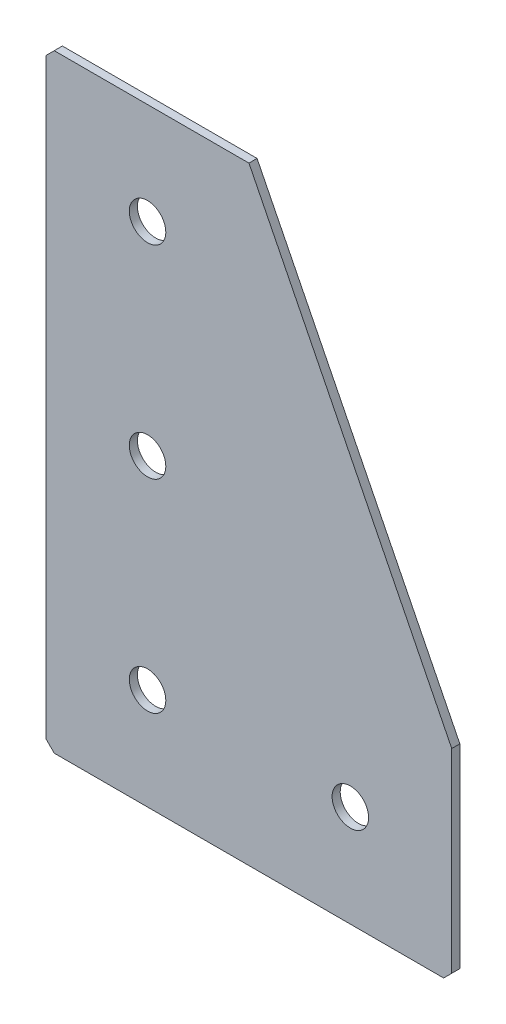
SolidWorks part; units mm, degrees
material "Простая углеродистая сталь"
ref_plane "Спереди(Плоскость XY)" through (0, 0, 0) normal (0, 0, 1) x (1, 0, 0)
ref_plane "Сверху(Плоскость XZ)" through (0, 0, 0) normal (0, 1, 0) x (1, 0, 0)
ref_plane "Справа(Плоскость ZY)" through (0, 0, 0) normal (1, 0, 0) x (0, 0, -1)
sketch "Эскиз1" plane through (0, 0, 0) normal (0, 0, -1) x (1, 0, 0)
  line L0 (0, 0) -> (0, 150)
  line L1 (0, 150) -> (100, 150)
  line L2 (100, 150) -> (100, 100)
  line L3 (100, 100) -> (50, 100) construction
  line L4 (50, 100) -> (50, 0) construction
  line L5 (50, 0) -> (0, 0)
  line L6 (100, 100) -> (50, 0)
  dimension "D1" = 150
  dimension "D2" = 50
  dimension "D3" = 50
  dimension "D4" = 50
extrude "Бобышка-Вытянуть1" add sketch "Эскиз1" along normal blind 2
hole_wizard "Отверстие с зазором M81" positions "Эскиз2" profile "Эскиз3" hole size "M8" standard "DIN" end condition through all
sketch "Эскиз2" plane through (0, 0, -2) normal (0, 0, -1) x (1, 0, 0)
  line L0 (25, 0) -> (25, 150) construction
  line L1 (0, 0) -> (50, 0) construction
  line L2 (100, 150) -> (0, 150) construction
  line L3 (100, 125) -> (0, 125) construction
  line L4 (100, 100) -> (100, 150) construction
  line L5 (0, 150) -> (0, 0) construction
  point P0 (75, 125)
  point P2 (25, 125)
  point P4 (25, 75)
  point P6 (25, 25)
  dimension "D1" = 50
  dimension "D2" = 50
  dimension "D3" = 50
  dimension "D4" = 25
sketch "Эскиз3" plane through (75, -125, -2) normal (1, 0, 0) x (0, 1, 0)
  line L0 (0, 0) -> (0, 2)
  line L1 (0, 2) -> (4.5, 2)
  line L2 (4.5, 2) -> (4.5, 0)
  line L5 (4.5, 0) -> (0, 0)
  line L11 (0, -6.35) -> (0, 107.95) construction
  dimension "Диаметр сквозного отверстия" = 9
  dimension "Глубина сквозного отверстия" = 2
chamfer "Фаска1" distance 2 angle 45 3 edges at (0, 0, -1) (100, -150, -1) (0, -150, -1)
